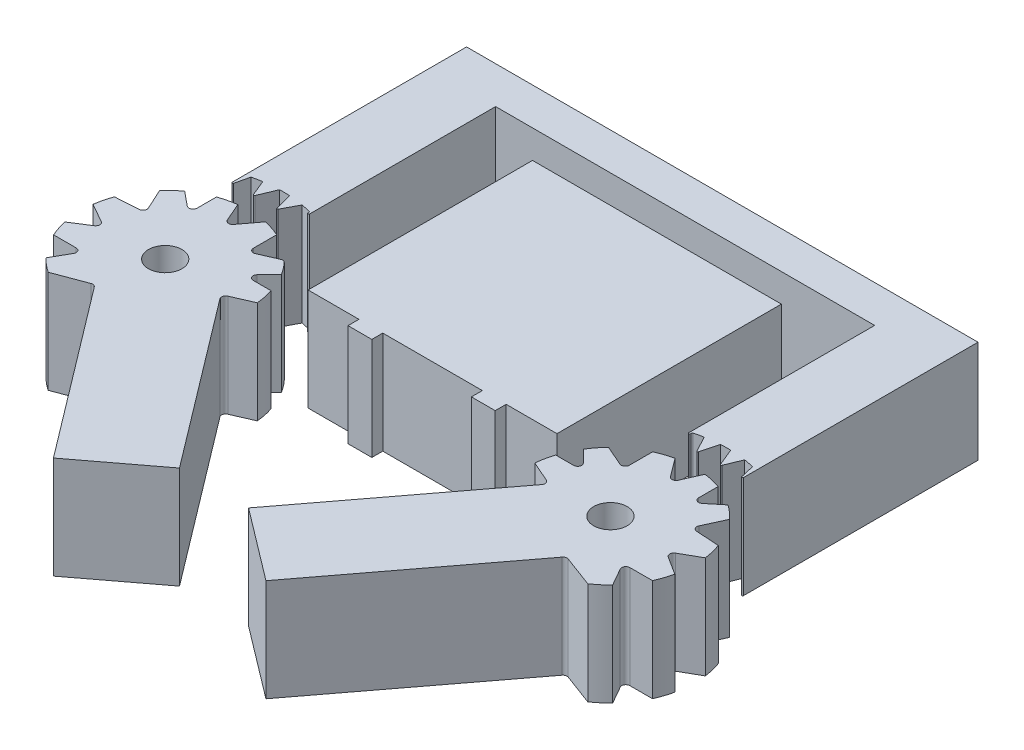
SolidWorks part; units mm, degrees
ref_plane "Front Plane" through (0, 0, 0) normal (0, 0, 1) x (1, 0, 0)
ref_plane "Top Plane" through (0, 0, 0) normal (0, 1, 0) x (1, 0, 0)
ref_plane "Right Plane" through (0, 0, 0) normal (1, 0, 0) x (0, 0, -1)
sketch "Sketch1" plane through (0, 0, 0) normal (0, 1, 0) x (1, 0, 0)
  line L7 (0, 55) -> (50, 55)
  line L8 (50, 14.7221) -> (50, 15.9859)
  line L9 (43.5277, 51.3683) -> (6.4723, 51.3683)
  line L10 (6.4723, 51.3683) -> (6.4723, 33.3075)
  line L11 (8.9628, 22.0246) -> (21.6235, 5.311)
  line L12 (21.6235, 5.311) -> (14.6124, 0)
  line L13 (14.6124, 0) -> (1.9517, 16.7136)
  line L14 (0, 33.3075) -> (0, 55)
  line L17 (50, 31.3885) -> (50, 55)
  line L19 (8.9628, 22.0246) -> (11.4377, 23.1077)
  line L22 (11.089, 24.8011) -> (8.3957, 24.8011)
  line L23 (8.3957, 24.8011) -> (10.2205, 26.6755)
  line L24 (9.1542, 28.0364) -> (6.6217, 26.9281)
  line L25 (0, 33.3075) -> (0, 31.3885)
  line L26 (6.4723, 33.3075) -> (6.4723, 31.3885)
  line L27 (6.6217, 26.9281) -> (6.6217, 29.8148)
  line L28 (4.9796, 30.3558) -> (3.2361, 28.0345)
  line L29 (3.2361, 28.0345) -> (2.1626, 30.4721)
  line L30 (0.4815, 30.0683) -> (0.4815, 27.3293)
  line L31 (0.4815, 27.3293) -> (-1.5596, 29.0031)
  line L32 (-2.8524, 27.8551) -> (-1.6651, 25.2758)
  line L33 (-1.6651, 25.2758) -> (-4.5173, 25.0939)
  line L34 (-4.9294, 23.4148) -> (-2.4905, 22.0246)
  line L35 (-2.4905, 22.0246) -> (-4.8151, 20.5422)
  line L36 (-4.2709, 18.9012) -> (-1.3802, 18.9012)
  line L37 (-1.3802, 18.9012) -> (-2.7004, 16.5851)
  line L38 (-1.3771, 15.4723) -> (1.9517, 16.7136)
  line L39 (0, 31.3885) -> (0.4815, 33.4377)
  line L40 (1.4451, 33.6327) -> (2.1626, 31.8876)
  line L41 (2.1626, 31.8876) -> (2.948, 33.7697)
  line L42 (3.9311, 33.7523) -> (4.433, 31.873)
  line L43 (4.433, 31.873) -> (5.339, 33.579)
  line L44 (6.2969, 33.3575) -> (6.4723, 31.3885)
  line L45 (17.8043, 26.6755) -> (12.8353, 26.6755)
  line L46 (37.1647, 48.6123) -> (12.8353, 48.6123)
  line L48 (29.867, 26.6755) -> (20.133, 26.6755)
  line L49 (12.8353, 48.6123) -> (12.8353, 26.6755)
  line L51 (17.8043, 26.6755) -> (17.8043, 25.6051)
  line L52 (17.8043, 25.6051) -> (20.133, 25.6051)
  line L53 (20.133, 26.6755) -> (20.133, 25.6051)
  line L54 (29.867, 26.6755) -> (29.867, 25.6051)
  line L55 (32.1957, 25.6051) -> (29.867, 25.6051)
  line L56 (32.1957, 26.6755) -> (32.1957, 25.6051)
  line L57 (32.1957, 26.6755) -> (37.1647, 26.6755)
  line L58 (28.3765, 5.311) -> (35.3876, 0)
  line L59 (41.0372, 22.0246) -> (28.3765, 5.311)
  line L65 (37.1647, 48.6123) -> (37.1647, 26.6755)
  line L66 (43.7031, 33.3575) -> (43.5277, 31.3885)
  line L67 (45.567, 31.873) -> (44.661, 33.579)
  line L68 (46.0689, 33.7523) -> (45.567, 31.873)
  line L69 (47.8374, 31.8876) -> (47.052, 33.7697)
  line L70 (48.5549, 33.6327) -> (47.8374, 31.8876)
  line L71 (50, 31.3885) -> (49.5185, 33.4377)
  line L72 (51.3771, 15.4723) -> (48.0483, 16.7136)
  line L73 (51.3802, 18.9012) -> (52.7004, 16.5851)
  line L74 (54.2709, 18.9012) -> (51.3802, 18.9012)
  line L75 (52.4905, 22.0246) -> (54.8151, 20.5422)
  line L76 (54.9294, 23.4148) -> (52.4905, 22.0246)
  line L77 (51.6651, 25.2758) -> (54.5173, 25.0939)
  line L78 (52.8524, 27.8551) -> (51.6651, 25.2758)
  line L79 (49.5185, 27.3293) -> (51.5596, 29.0031)
  line L80 (49.5185, 30.0683) -> (49.5185, 27.3293)
  line L81 (46.7639, 28.0345) -> (47.8374, 30.4721)
  line L82 (45.0204, 30.3558) -> (46.7639, 28.0345)
  line L83 (43.3783, 26.9281) -> (43.3783, 29.8148)
  line L84 (43.5277, 33.3075) -> (43.5277, 31.3885)
  line L85 (50, 33.3075) -> (50, 31.3885)
  line L86 (40.8458, 28.0364) -> (43.3783, 26.9281)
  line L87 (41.6043, 24.8011) -> (39.7795, 26.6755)
  line L88 (38.911, 24.8011) -> (41.6043, 24.8011)
  line L89 (41.0372, 22.0246) -> (38.5623, 23.1077)
  line L91 (50, 33.3075) -> (50, 55)
  line L92 (35.3876, 0) -> (48.0483, 16.7136)
  line L93 (43.5277, 51.3683) -> (43.5277, 33.3075)
  arc A4 (11.4377, 23.1077) -> (11.089, 24.8011) centre (3.2361, 22.3012) ccw
  arc A5 (6.2969, 33.3575) -> (5.339, 33.579) centre (3.2361, 22.3012) ccw
  circle A7 centre (3.2361, 22.3012) radius 1.6349
  circle A8 centre (3.2361, 22.3012) radius 1.6349
  arc A9 (10.2205, 26.6755) -> (9.1542, 28.0364) centre (3.2361, 22.3012) ccw
  arc A11 (6.6217, 29.8148) -> (4.9796, 30.3558) centre (3.2361, 22.3012) ccw
  arc A12 (2.1626, 30.4721) -> (0.4815, 30.0683) centre (3.2361, 22.3012) ccw
  arc A13 (-1.5596, 29.0031) -> (-2.8524, 27.8551) centre (3.2361, 22.3012) ccw
  arc A14 (-4.5173, 25.0939) -> (-4.9294, 23.4148) centre (3.2361, 22.3012) ccw
  arc A15 (-4.8151, 20.5422) -> (-4.2709, 18.9012) centre (3.2361, 22.3012) ccw
  arc A16 (-2.7004, 16.5851) -> (-1.3771, 15.4723) centre (3.2361, 22.3012) ccw
  arc A17 (1.4451, 33.6327) -> (0.4815, 33.4377) centre (3.2361, 22.3012) ccw
  arc A18 (3.9311, 33.7523) -> (2.948, 33.7697) centre (3.2361, 22.3012) ccw
  arc A19 (46.0689, 33.7523) -> (47.052, 33.7697) centre (46.7639, 22.3012) cw
  arc A20 (48.5549, 33.6327) -> (49.5185, 33.4377) centre (46.7639, 22.3012) cw
  arc A21 (52.7004, 16.5851) -> (51.3771, 15.4723) centre (46.7639, 22.3012) cw
  arc A22 (54.8151, 20.5422) -> (54.2709, 18.9012) centre (46.7639, 22.3012) cw
  arc A23 (54.5173, 25.0939) -> (54.9294, 23.4148) centre (46.7639, 22.3012) cw
  arc A24 (51.5596, 29.0031) -> (52.8524, 27.8551) centre (46.7639, 22.3012) cw
  arc A25 (47.8374, 30.4721) -> (49.5185, 30.0683) centre (46.7639, 22.3012) cw
  arc A26 (43.3783, 29.8148) -> (45.0204, 30.3558) centre (46.7639, 22.3012) cw
  arc A27 (39.7795, 26.6755) -> (40.8458, 28.0364) centre (46.7639, 22.3012) cw
  circle A28 centre (46.7639, 22.3012) radius 1.6349
  circle A29 centre (46.7639, 22.3012) radius 1.6349
  arc A30 (43.7031, 33.3575) -> (44.661, 33.579) centre (46.7639, 22.3012) cw
  arc A31 (38.5623, 23.1077) -> (38.911, 24.8011) centre (46.7639, 22.3012) cw
  circle A32 centre (3.2361, 22.3012) radius 1.0478
  circle A33 centre (46.7639, 22.3012) radius 1.0478
  point P80 (25, 51.3683)
extrude "Boss-Extrude1" add sketch "Sketch1" along normal blind 10 contours L65 L46 L49 L45 L51 L52 L53 L48 L54 L55 L56 L57 | L37 A16 L38 L13 L12 L11 L19 A4 L22 L23 A9 L24 L27 A11 L28 L29 A12 L30 L31 A13 L32 L33 A14 L34 L35 A15 L36 A7 | L66 A30 L67 L68 A19 L69 L70 A20 L71 L17 L7 L14 L25 L39 A17 L40 L41 A18 L42 L43 A5 L44 L26 L10 L9 L93 L84 | A31 L89 L59 L58 L92 L72 A21 L73 L74 A22 L75 L76 A23 L77 L78 A24 L79 L80 A25 L81 L82 A26 L83 L86 A27 L87 L88 A28
fillet "Fillet3" radius 0.08 9 edges at (43.5277, 5, -31.3885) (43.7031, 5, -33.3575) (50, 5, -31.3885) (47.8374, 5, -31.8876) (45.567, 5, -31.873) (6.4723, 5, -31.3885) (4.433, 5, -31.873) (2.1626, 5, -31.8876) (0, 5, -31.3885)
fillet "Fillet4" radius 0.4 10 edges at (1.9517, 5, -16.7136) (-1.3802, 5, -18.9012) (9.1542, 5, -28.0364) (-2.4905, 5, -22.0246) (-1.6651, 5, -25.2758) (8.9628, 5, -22.0246) (8.3957, 5, -24.8011) (6.6217, 5, -26.9281) (3.2361, 5, -28.0345) (0.4815, 5, -27.3293)
fillet "Fillet5" radius 0.4 9 edges at (41.6043, 5, -24.8011) (41.0372, 5, -22.0246) (43.3783, 5, -26.9281) (46.7639, 5, -28.0345) (49.5185, 5, -27.3293) (51.6651, 5, -25.2758) (52.4905, 5, -22.0246) (51.3802, 5, -18.9012) (48.0483, 5, -16.7136)
